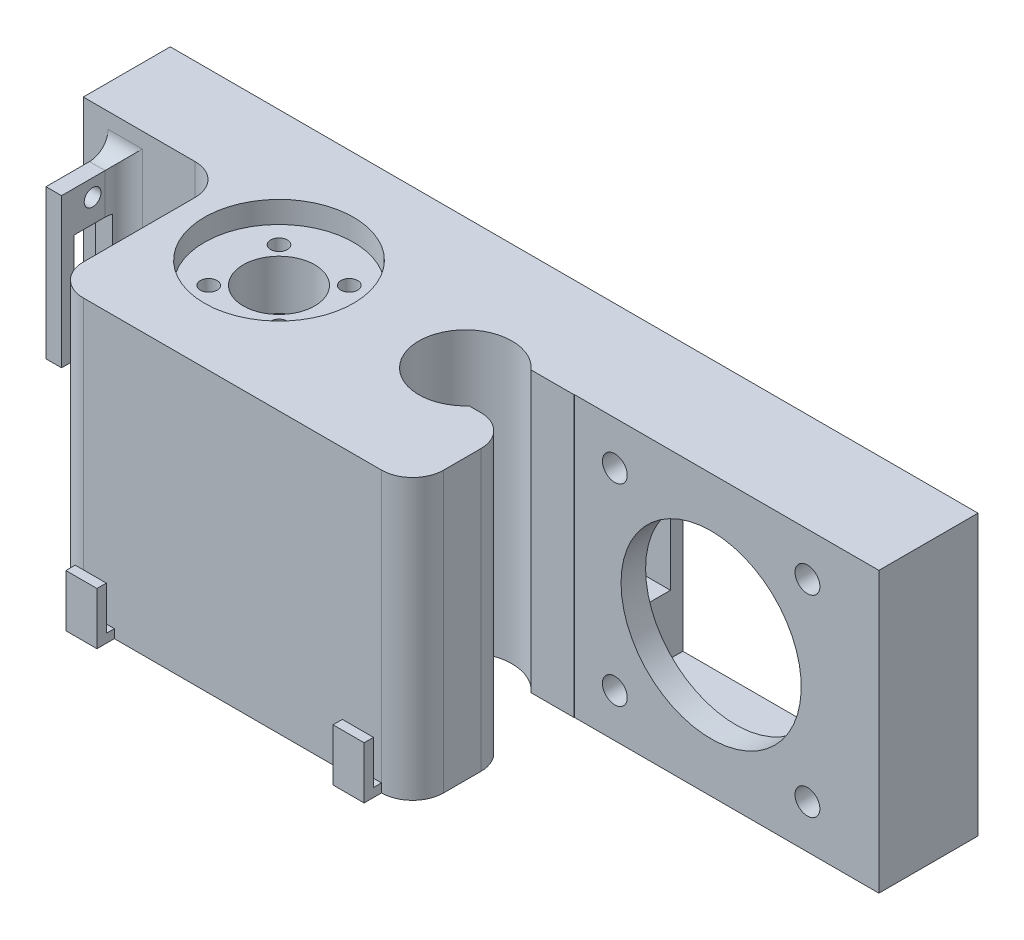
SolidWorks part; units mm, degrees
ref_plane "Front Plane" through (0, 0, 0) normal (0, 0, 1) x (1, 0, 0)
ref_plane "Top Plane" through (0, 0, 0) normal (0, 1, 0) x (1, 0, 0)
ref_plane "Right Plane" through (0, 0, 0) normal (1, 0, 0) x (0, 0, -1)
sketch "Sketch1" plane through (0, 0, 0) normal (0, 0, 1) x (1, 0, 0)
  line L1 (0, 0) -> (130, 0)
  line L2 (0, 0) -> (0, 45)
  line L3 (0, 45) -> (130, 45)
  line L4 (130, 0) -> (130, 45)
  dimension "D1" = 45
  dimension "D2" = 130
extrude "Boss-Extrude1" add sketch "Sketch1" along normal blind 42
sketch "Sketch2" plane through (0, 0, 0) normal (-1, 0, 0) x (0, 0, 1)
  line L0 (42, 22.5) -> (0, 22.5) construction
  line L5 (42, 45) -> (42, 0) construction
  line L6 (0, 45) -> (0, 0) construction
  line L8 (2, 11.5) -> (12, 11.5)
  line L9 (2, 11.5) -> (2, 33.5)
  line L10 (2, 33.5) -> (12, 33.5)
  line L11 (12, 11.5) -> (12, 33.5)
  line L12 (2, 11.5) -> (12, 33.5) construction
  line L13 (2, 33.5) -> (12, 11.5) construction
  point P10 (7, 22.5)
  dimension "D1" = 2
  dimension "D2" = 22
  dimension "D3" = 10
extrude "Cut-Extrude1" cut sketch "Sketch2" against normal blind 115
sketch "Sketch3" plane through (0, 0, 0) normal (0, 0, -1) x (-1, 0, 0)
  line L1 (-118.5, 38) -> (-87.5, 38) construction
  line L2 (-118.5, 38) -> (-118.5, 7) construction
  line L3 (-118.5, 7) -> (-87.5, 7) construction
  line L4 (-87.5, 38) -> (-87.5, 7) construction
  line L5 (-118.5, 38) -> (-87.5, 7) construction
  line L6 (-118.5, 7) -> (-87.5, 38) construction
  line L7 (-123.5, 43) -> (-82.5, 43)
  line L8 (-123.5, 43) -> (-123.5, 2)
  line L9 (-123.5, 2) -> (-82.5, 2)
  line L10 (-82.5, 43) -> (-82.5, 2)
  line L11 (-123.5, 43) -> (-82.5, 2) construction
  line L12 (-123.5, 2) -> (-82.5, 43) construction
  point P4 (-103, 22.5)
  point P11 (-103, 22.5)
  dimension "D1" = 5
  dimension "D2" = 5
extrude "Cut-Extrude2" cut sketch "Sketch3" against normal blind 12
sketch "Sketch5" plane through (0, 0, 42) normal (0, 0, 1) x (1, 0, 0)
  line L0 (0, 0) -> (130, 0) construction
  line L1 (130, 45) -> (81, 45)
  line L2 (130, 45) -> (130, 0)
  line L3 (130, 0) -> (81, 0)
  line L4 (81, 45) -> (81, 0)
  line L5 (130, 45) -> (81, 0) construction
  line L6 (130, 0) -> (81, 45) construction
  point P4 (105.5, 22.5)
  dimension "D1" = 49
extrude "Cut-Extrude3" cut sketch "Sketch5" against normal up to surface (26.05 mm away)
sketch "Sketch6" plane through (0, 0, 0) normal (0, 0, -1) x (-1, 0, 0)
  line L1 (-118.5, 38) -> (-87.5, 38) construction
  line L2 (-118.5, 38) -> (-118.5, 7) construction
  line L3 (-118.5, 7) -> (-87.5, 7) construction
  line L4 (-87.5, 38) -> (-87.5, 7) construction
  line L5 (-118.5, 38) -> (-87.5, 7) construction
  line L6 (-118.5, 7) -> (-87.5, 38) construction
  circle A0 centre (-118.5, 38) radius 2
  circle A1 centre (-87.5, 38) radius 2
  circle A2 centre (-87.5, 7) radius 2
  circle A3 centre (-118.5, 7) radius 2
  point P4 (-103, 22.5)
  dimension "D1" = 4
  dimension "D2" = 4
  dimension "D3" = 4
  dimension "D4" = 4
extrude "Cut-Extrude4" cut sketch "Sketch6" against normal through all
sketch "Sketch7" plane through (0, 45, 0) normal (0, 1, 0) x (1, 0, 0)
  circle A0 centre (38.5, -21) radius 12
  dimension "D1" = 24
extrude "Cut-Extrude5" cut sketch "Sketch7" against normal blind 3.5
sketch "Sketch8" plane through (0, 45, 0) normal (0, 1, 0) x (1, 0, 0)
  circle A0 centre (68.5, -21) radius 7.5
  dimension "D1" = 15
extrude "Cut-Extrude6" cut sketch "Sketch8" against normal through all
sketch "Sketch10" plane through (0, 45, 0) normal (0, 1, 0) x (1, 0, 0)
  line L1 (0, -42) -> (23, -42)
  line L2 (0, -42) -> (0, -14)
  line L3 (0, -14) -> (23, -14)
  line L4 (23, -42) -> (23, -14)
  line L5 (0, -42) -> (23, -14) construction
  line L6 (0, -14) -> (23, -42) construction
  point P4 (11.5, -28)
  dimension "D1" = 28
  dimension "D2" = 23
extrude "Cut-Extrude7" cut sketch "Sketch10" against normal through all
fillet "Fillet1" radius 5 2 edges at (23, 22.5, 42) (81, 22.5, 42)
sketch "Sketch11" plane through (0, 41.5, 0) normal (0, 1, 0) x (1, 0, 0)
  circle A0 centre (38.5, -21) radius 5.75
  dimension "D1" = 11.5
extrude "Cut-Extrude8" cut sketch "Sketch11" against normal through all
sketch "Sketch12" plane through (0, 41.5, 0) normal (0, 1, 0) x (1, 0, 0)
  circle A0 centre (32.8431, -15.3431) radius 1.35
  circle A1 centre (44.1569, -15.3431) radius 1.35
  circle A2 centre (44.1569, -26.6569) radius 1.35
  circle A3 centre (32.8431, -26.6569) radius 1.35
  dimension "D1" = 2.7
extrude "Cut-Extrude9" cut sketch "Sketch12" against normal blind 20
sketch "Sketch14" plane through (0, 0, 0) normal (0, 0, -1) x (-1, 0, 0)
  line L0 (0, 22.5) -> (-82.5, 22.5) construction
  line L1 (-75, 7.5) -> (-15, 7.5) construction
  line L2 (-75, 7.5) -> (-75, 37.5) construction
  line L3 (-75, 37.5) -> (-15, 37.5) construction
  line L4 (-15, 7.5) -> (-15, 37.5) construction
  line L5 (-75, 7.5) -> (-15, 37.5) construction
  line L6 (-75, 37.5) -> (-15, 7.5) construction
  line L7 (0, 45) -> (0, 0) construction
  line L8 (-82.5, 2) -> (-82.5, 43) construction
  circle A0 centre (-75, 37.5) radius 1.75
  circle A1 centre (-15, 37.5) radius 1.75
  circle A2 centre (-15, 7.5) radius 1.75
  circle A3 centre (-75, 7.5) radius 1.75
  point P0 (-45, 22.5)
  dimension "D4" = 3.5
  dimension "D1" = 60
  dimension "D2" = 30
  dimension "D3" = 15
extrude "Cut-Extrude11" cut sketch "Sketch14" against normal blind 12
sketch "Sketch15" plane through (0, 45, 0) normal (0, 1, 0) x (1, 0, 0)
  line L0 (61, -21) -> (86.2394, -21) construction
  line L2 (98.575, -16) -> (66.113, -16)
  line L3 (98.575, -16) -> (98.575, -26)
  line L4 (98.575, -26) -> (66.113, -26)
  line L5 (66.113, -16) -> (66.113, -26)
  line L6 (98.575, -16) -> (66.113, -26) construction
  line L7 (98.575, -26) -> (66.113, -16) construction
  circle A0 centre (68.5, -21) radius 7.5 construction
  point P5 (82.344, -21)
  dimension "D1" = 10
extrude "Cut-Extrude12" cut sketch "Sketch15" against normal through all
fillet "Fillet2" radius 5 1 edges at (81, 22.5, 26)
fillet "Fillet3" radius 5 1 edges at (23, 22.5, 14)
sketch "Sketch16" plane through (0, 0, 0) normal (0, -1, 0) x (1, 0, 0)
  circle A0 centre (38.5, 21) radius 12.5
  dimension "D1" = 25
extrude "Cut-Extrude13" cut sketch "Sketch16" against normal up to surface (33.5 mm away) up to face at (41.25, 33.5, 7)
sketch "Sketch17" plane through (0, 0, 14) normal (0, 0, 1) x (1, 0, 0)
  line L1 (4, 39.5) -> (6.5, 39.5)
  line L2 (4, 39.5) -> (4, 15.5)
  line L3 (4, 15.5) -> (6.5, 15.5)
  line L4 (6.5, 39.5) -> (6.5, 15.5)
  line L5 (4, 39.5) -> (6.5, 15.5) construction
  line L6 (4, 15.5) -> (6.5, 39.5) construction
  point P4 (5.25, 27.5)
  dimension "D1" = 24
  dimension "D2" = 2.5
extrude "Boss-Extrude2" add sketch "Sketch17" along normal blind 10
sketch "Sketch18" plane through (4, 0, 0) normal (-1, 0, 0) x (0, 0, 1)
  circle A0 centre (19, 36.775) radius 1.35
  circle A1 centre (19, 17.725) radius 1.35
  dimension "D1" = 2.7
extrude "Cut-Extrude14" cut sketch "Sketch18" against normal blind 10
fillet "Fillet4" radius 3 1 edges at (6.5, 27.5, 14)
fillet "Fillet5" radius 3 2 edges at (6.75, 39.5, 14) (6.75, 15.5, 14)
sketch "Sketch20" plane through (0, 0, 42) normal (0, 0, 1) x (1, 0, 0)
  line L1 (28, 0) -> (33, 0)
  line L2 (28, 0) -> (28, 1.4)
  line L3 (28, 1.4) -> (33, 1.4)
  line L4 (33, 0) -> (33, 1.4)
  line L5 (28, 0) -> (33, 1.4) construction
  line L6 (28, 1.4) -> (33, 0) construction
  line L7 (76, 0) -> (71, 0)
  line L8 (76, 0) -> (76, 1.4)
  line L9 (76, 1.4) -> (71, 1.4)
  line L10 (71, 0) -> (71, 1.4)
  line L11 (76, 0) -> (71, 1.4) construction
  line L12 (76, 1.4) -> (71, 0) construction
  point P4 (30.5, 0.7)
  point P10 (73.5, 0.7)
  dimension "D1" = 1.4
  dimension "D2" = 5
  dimension "D3" = 5
  dimension "D4" = 1.4
extrude "Boss-Extrude3" add sketch "Sketch20" along normal blind 2.8
sketch "Sketch22" plane through (23, 0, 0) normal (-1, 0, 0) x (0, 0, 1)
  line L0 (28, 45) -> (28, 0) construction
  line L1 (25.5, 0) -> (30.5, 0)
  line L2 (25.5, 0) -> (25.5, 1.4)
  line L3 (25.5, 1.4) -> (30.5, 1.4)
  line L4 (30.5, 0) -> (30.5, 1.4)
  line L5 (25.5, 0) -> (30.5, 1.4) construction
  line L6 (25.5, 1.4) -> (30.5, 0) construction
  line L7 (37, 45) -> (19, 45) construction
  line L8 (37, 0) -> (19, 0) construction
  point P4 (28, 0.7)
  dimension "D1" = 1.4
  dimension "D2" = 5
extrude "Boss-Extrude4" add sketch "Sketch22" along normal blind 2.8
sketch "Sketch25" plane through (0, 1.4, 0) normal (0, 1, 0) x (1, 0, 0)
  line L0 (20.2, -25.5) -> (23, -25.5) construction
  line L1 (20.2, -25.5) -> (21.7, -25.5)
  line L2 (20.2, -25.5) -> (20.2, -30.5)
  line L3 (20.2, -30.5) -> (21.7, -30.5)
  line L4 (21.7, -25.5) -> (21.7, -30.5)
  line L5 (20.2, -25.5) -> (21.7, -30.5) construction
  line L6 (20.2, -30.5) -> (21.7, -25.5) construction
  line L7 (20.2, -30.5) -> (23, -30.5) construction
  line L8 (23, -37) -> (23, -19) construction
  line L9 (76, -44.8) -> (76, -42) construction
  line L10 (76, -43.3) -> (71, -43.3)
  line L11 (76, -43.3) -> (76, -44.8)
  line L12 (76, -44.8) -> (71, -44.8)
  line L13 (71, -43.3) -> (71, -44.8)
  line L14 (76, -43.3) -> (71, -44.8) construction
  line L15 (76, -44.8) -> (71, -43.3) construction
  line L16 (71, -44.8) -> (71, -42) construction
  line L17 (33, -44.8) -> (33, -42) construction
  line L18 (33, -43.3) -> (28, -43.3)
  line L19 (33, -43.3) -> (33, -44.8)
  line L20 (33, -44.8) -> (28, -44.8)
  line L21 (28, -43.3) -> (28, -44.8)
  line L22 (33, -43.3) -> (28, -44.8) construction
  line L23 (33, -44.8) -> (28, -43.3) construction
  line L24 (28, -44.8) -> (28, -42) construction
  line L25 (76, -42) -> (71, -42) construction
  line L26 (33, -42) -> (28, -42) construction
  point P4 (20.95, -28)
  point P15 (73.5, -44.05)
  point P24 (30.5, -44.05)
  dimension "D1" = 1.3
  dimension "D2" = 1.5
  dimension "D3" = 1.5
  dimension "D4" = 1.3
  dimension "D5" = 1.5
  dimension "D6" = 1.3
extrude "Boss-Extrude5" add sketch "Sketch25" along normal blind 7
sketch "Sketch26" plane through (0, 0, 12) normal (0, 0, -1) x (-1, 0, 0)
  line L0 (-103, 43) -> (-103, 2) construction
  line L1 (-82.5, 43) -> (-123.5, 43) construction
  line L2 (-123.5, 2) -> (-82.5, 2) construction
  line L3 (-123.5, 22.5) -> (-82.5, 22.5) construction
  line L4 (-123.5, 43) -> (-123.5, 2) construction
  line L5 (-82.5, 2) -> (-82.5, 43) construction
  circle A0 centre (-103, 22.5) radius 14.5
  dimension "D1" = 29
extrude "Cut-Extrude15" cut sketch "Sketch26" against normal blind 10
sketch "Sketch27" plane through (4, 0, 0) normal (-1, 0, 0) x (0, 0, 1)
  line L0 (19, 45) -> (19, 0) construction
  line L1 (16, 22) -> (22, 22)
  line L2 (16, 22) -> (16, 33)
  line L3 (16, 33) -> (22, 33)
  line L4 (22, 22) -> (22, 33)
  line L5 (16, 22) -> (22, 33) construction
  line L6 (16, 33) -> (22, 22) construction
  point P0 (19, 27.5)
  dimension "D1" = 11
  dimension "D2" = 6
extrude "Cut-Extrude16" cut sketch "Sketch27" against normal blind 10
